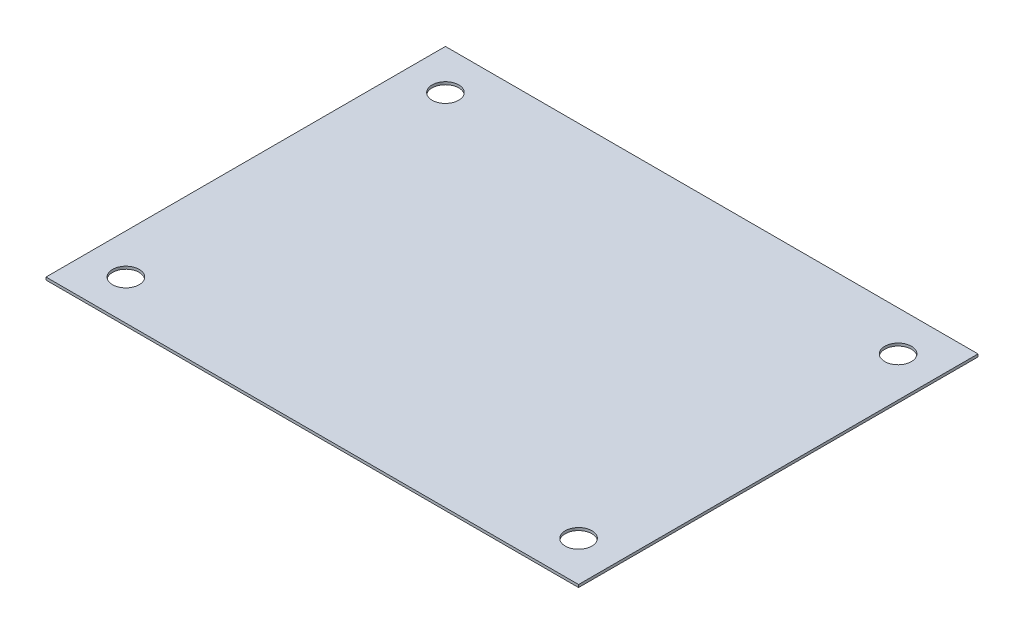
SolidWorks part; units mm, degrees
ref_plane "前视基准面" through (0, 0, 0) normal (0, 0, 1) x (1, 0, 0)
ref_plane "上视基准面" through (0, 0, 0) normal (0, 1, 0) x (1, 0, 0)
ref_plane "右视基准面" through (0, 0, 0) normal (1, 0, 0) x (0, 0, -1)
sketch "草图1" plane through (0, 0, 0) normal (0, 1, 0) x (1, 0, 0)
  line L0 (-200, 0) -> (200, 0) construction
  line L1 (-200, 150) -> (200, 150)
  line L2 (-200, 150) -> (-200, -150)
  line L3 (-200, -150) -> (200, -150)
  line L4 (200, 150) -> (200, -150)
  line L5 (0, 150) -> (0, -150) construction
  circle A0 centre (-170, 120) radius 10
  circle A1 centre (-170, -120) radius 10
  circle A2 centre (170, 120) radius 10
  circle A3 centre (170, -120) radius 10
  dimension "D3" = 20
  dimension "D5" = 170
  dimension "D1" = 400
  dimension "D2" = 300
  dimension "D4" = 120
extrude "凸台-拉伸1" add sketch "草图1" along normal blind 2
